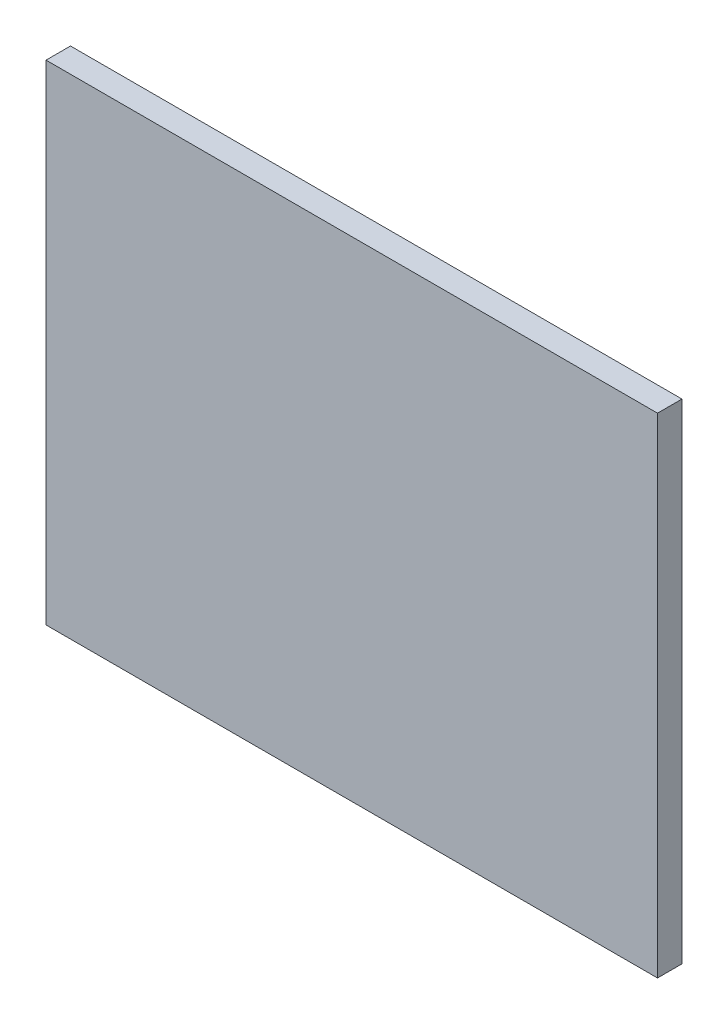
SolidWorks part; units mm, degrees
material "Glas"
ref_plane "Ebene vorne" through (0, 0, 0) normal (0, 0, 1) x (1, 0, 0)
ref_plane "Ebene oben" through (0, 0, 0) normal (0, 1, 0) x (1, 0, 0)
ref_plane "Ebene rechts" through (0, 0, 0) normal (1, 0, 0) x (0, 0, -1)
sketch "Skizze1" plane through (0, 0, 0) normal (0, 0, 1) x (1, 0, 0)
  line L1 (12.5, -10) -> (-12.5, -10)
  line L2 (12.5, -10) -> (12.5, 10)
  line L3 (12.5, 10) -> (-12.5, 10)
  line L4 (-12.5, -10) -> (-12.5, 10)
  line L5 (12.5, -10) -> (-12.5, 10) construction
  line L6 (12.5, 10) -> (-12.5, -10) construction
  point P0 (0, 0)
  dimension "D1" = 20
  dimension "D2" = 25
extrude "Aufsatz-Linear austragen1" add sketch "Skizze1" along normal blind 1
